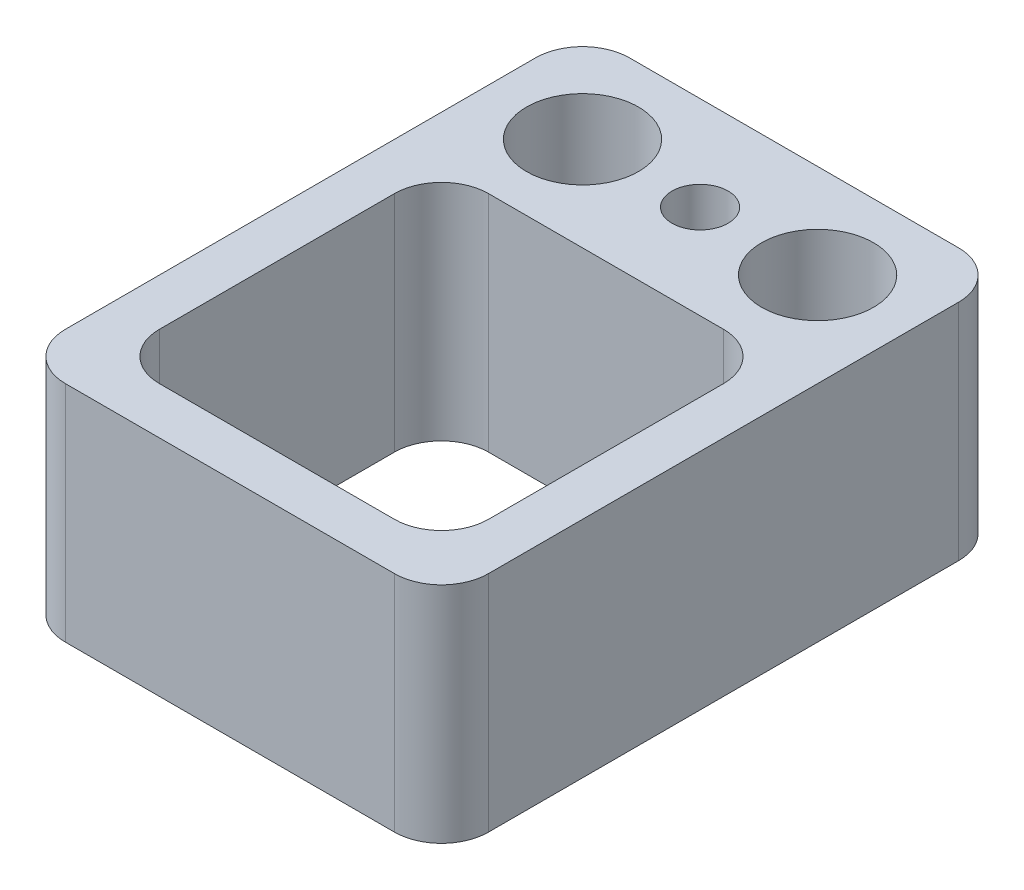
SolidWorks part; units mm, degrees
ref_plane "Front Plane" through (0, 0, 0) normal (0, 0, 1) x (1, 0, 0)
ref_plane "Top Plane" through (0, 0, 0) normal (0, 1, 0) x (1, 0, 0)
ref_plane "Right Plane" through (0, 0, 0) normal (1, 0, 0) x (0, 0, -1)
sketch "Sketch1" plane through (0, 0, 0) normal (0, 1, 0) x (1, 0, 0)
  line L1 (4.5, -6) -> (-4.5, -6)
  line L2 (4.5, -6) -> (4.5, 6)
  line L3 (4.5, 6) -> (-4.5, 6)
  line L4 (-4.5, -6) -> (-4.5, 6)
  line L5 (4.5, -6) -> (-4.5, 6) construction
  line L6 (4.5, 6) -> (-4.5, -6) construction
  point P0 (0, 0)
  dimension "D1" = 9
  dimension "D2" = 12
extrude "Extrude1" add sketch "Sketch1" along normal blind 4.7625
sketch "Sketch2" plane through (0, 4.7625, 0) normal (0, 1, 0) x (1, 0, 0)
  line L0 (-4.5, 6) -> (-4.5, -6) construction
  line L1 (-3.5, -5) -> (3.5, -5)
  line L2 (-3.5, -5) -> (-3.5, 2)
  line L3 (-3.5, 2) -> (3.5, 2)
  line L4 (3.5, -5) -> (3.5, 2)
  line L5 (-4.5, -6) -> (4.5, -6) construction
  dimension "D1" = 7
  dimension "D2" = 7
  dimension "D3" = 1
  dimension "D4" = 1
extrude "Extrude2" cut sketch "Sketch2" against normal through all
hole_wizard "#0-80 Tapped Hole1" positions "3DSketch5" profile "Sketch9" tap size "#0-80" standard "Ansi Inch" end condition through all
sketch3d "3DSketch5"
  line L0 (4.5, 4.7625, -6) -> (-4.5, 4.7625, -6) construction
  line L1 (4.5, 4.7625, 6) -> (4.5, 4.7625, -6) construction
  point P0 (0, 4.7625, -4)
  dimension "D1" = 2
  dimension "D2" = 4.5
sketch "Sketch9" plane through (0, 4.7625, -4) normal (1, 0, 0) x (0, 0, 1)
  line L0 (0, 0) -> (0, 4.7625)
  line L1 (0, 4.7625) -> (0.5956, 4.7625)
  line L2 (0.5956, 4.7625) -> (0.5956, 0)
  line L5 (0.5956, 0) -> (0, 0)
  line L11 (0, -6.35) -> (0, 107.95) construction
  dimension "Thread Major Dia." = 1.1913
  dimension "Thru Tap Drill Depth" = 4.7625
hole_wizard "3/32 (0.09375) Diameter Hole1" positions "3DSketch6" profile "Sketch10" hole size "3/32" standard "Ansi Inch"
sketch3d "3DSketch6"
  line L0 (4.5, 4.7625, -6) -> (-4.5, 4.7625, -6) construction
  line L1 (4.5, 4.7625, 6) -> (4.5, 4.7625, -6) construction
  line L2 (-4.5, 4.7625, -6) -> (-4.5, 4.7625, 6) construction
  point P0 (-2.5, 4.7625, -4)
  point P2 (2.5, 4.7625, -4)
  dimension "D1" = 2
  dimension "D2" = 2
  dimension "D3" = 2
  dimension "D4" = 2
sketch "Sketch10" plane through (-2.5, 4.7625, -4) normal (1, 0, 0) x (0, 0, 1)
  line L0 (0, 0) -> (0, 10.7154)
  line L1 (0, 10.7154) -> (1.1906, 10)
  line L2 (1.1906, 10) -> (1.1906, 0)
  line L5 (1.1906, 0) -> (0, 0)
  line L10 (0, 10.7154) -> (-1.1906, 10) construction
  line L11 (0, -6.35) -> (0, 107.95) construction
  dimension "Hole Dia." = 2.3812
  dimension "Hole Depth" = 10
  dimension "Drill Angle" = 118
fillet "Fillet7" radius 1 8 edges at (-3.5, 2.3813, 5) (3.5, 2.3813, 5) (3.5, 2.3813, -2) (-3.5, 2.3813, -2) (-4.5, 2.3813, 6) (4.5, 2.3813, 6) (4.5, 2.3813, -6) (-4.5, 2.3813, -6)
